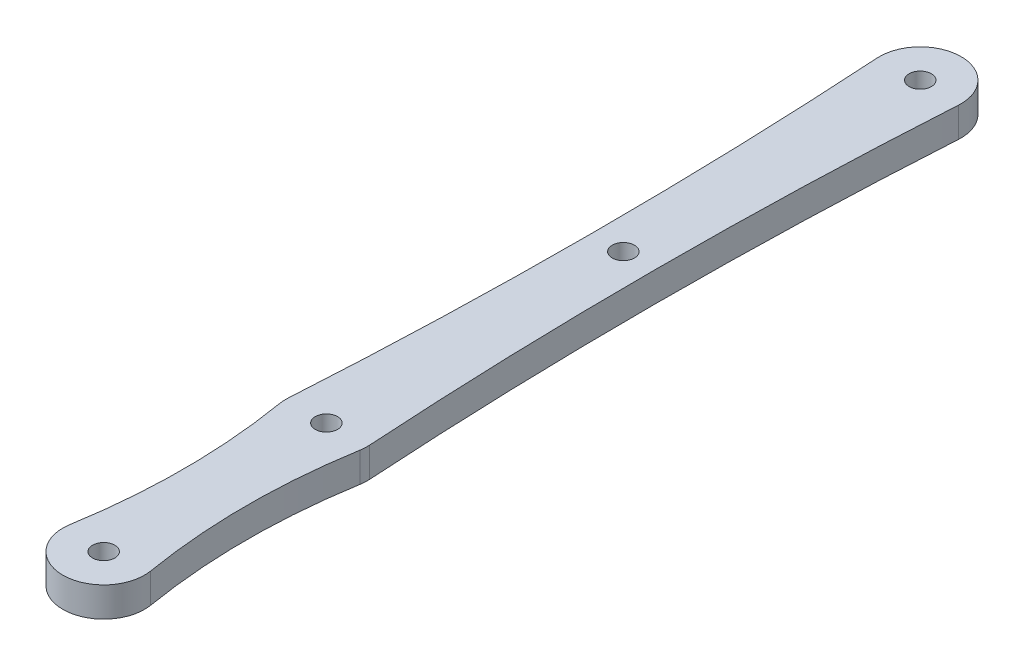
SolidWorks part; units mm, degrees
ref_plane "Front Plane" through (0, 0, 0) normal (0, 0, 1) x (1, 0, 0)
ref_plane "Top Plane" through (0, 0, 0) normal (0, 1, 0) x (1, 0, 0)
ref_plane "Right Plane" through (0, 0, 0) normal (1, 0, 0) x (0, 0, -1)
sketch "Sketch1" plane through (0, 0, 0) normal (0, 1, 0) x (1, 0, 0)
  line L0 (0, 0) -> (0, 110) construction
  line L3 (4.25, 70) -> (-4.25, 70) construction
  line L4 (4.25, 15) -> (-4.25, 15) construction
  circle A2 centre (0, 0) radius 1.5
  circle A3 centre (0, 110) radius 1.5
  arc A8 (-5.4241, 0.9103) -> (5.4241, 0.9103) centre (0, 0) ccw
  arc A9 (5.4893, 109.6566) -> (-5.4893, 109.6566) centre (0, 110) ccw
  circle A12 centre (0, 30) radius 1.5
  arc A13 (-5.4893, 30.3434) -> (-5.4241, 29.0897) centre (0, 30) ccw
  arc A14 (5.4241, 0.9103) -> (5.4241, 29.0897) centre (89.375, 15) cw
  arc A15 (5.4893, 30.3434) -> (5.4893, 109.6566) centre (639.375, 70) cw
  arc A16 (-5.4241, 0.9103) -> (-5.4241, 29.0897) centre (-89.375, 15) ccw
  arc A17 (-5.4893, 30.3434) -> (-5.4893, 109.6566) centre (-639.375, 70) ccw
  arc A18 (5.4241, 29.0897) -> (5.4893, 30.3434) centre (0, 30) ccw
  circle A19 centre (0, 70) radius 1.5
  point P26 (0, 15)
  point P27 (0, 70)
  dimension "D1" = 3
  dimension "D2" = 110
  dimension "D3" = 4
  dimension "D5" = 8.5
  dimension "D6" = 3
  dimension "D4" = 30
extrude "Boss-Extrude1" add sketch "Sketch1" along normal blind 4
